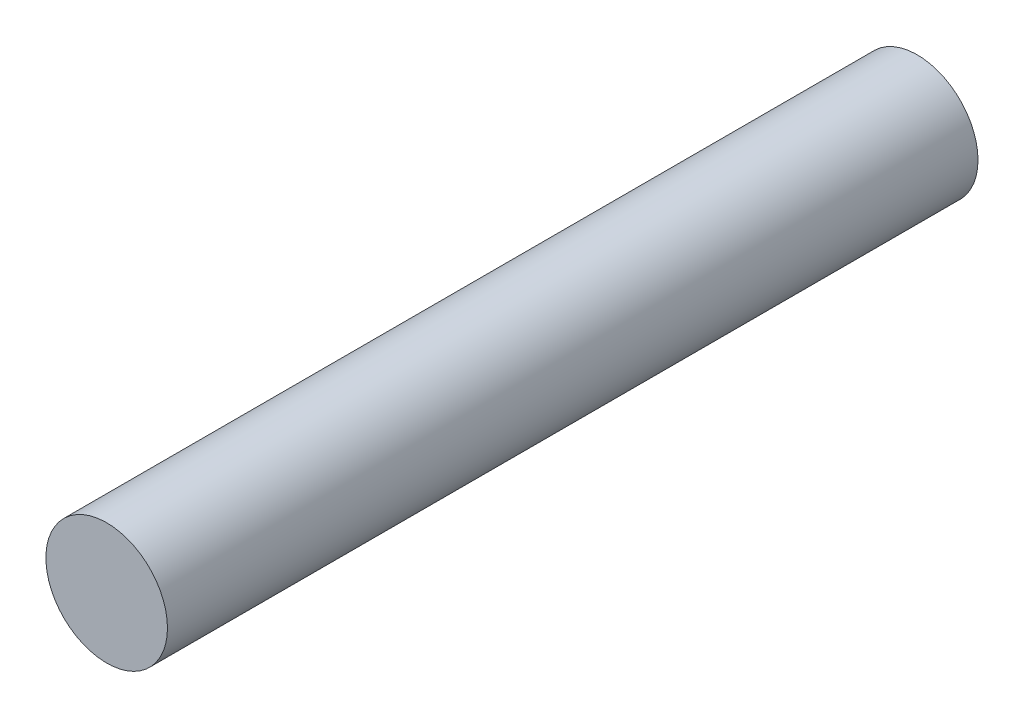
SolidWorks part; units mm, degrees
ref_plane "Front Plane" through (0, 0, 0) normal (0, 0, 1) x (1, 0, 0)
ref_plane "Top Plane" through (0, 0, 0) normal (0, 1, 0) x (1, 0, 0)
ref_plane "Right Plane" through (0, 0, 0) normal (1, 0, 0) x (0, 0, -1)
sketch "Sketch1" plane through (0, 0, 0) normal (0, 0, 1) x (1, 0, 0)
  circle A0 centre (0, 0) radius 3
  dimension "D1" = 6
extrude "Boss-Extrude1" add sketch "Sketch1" along normal blind 40
